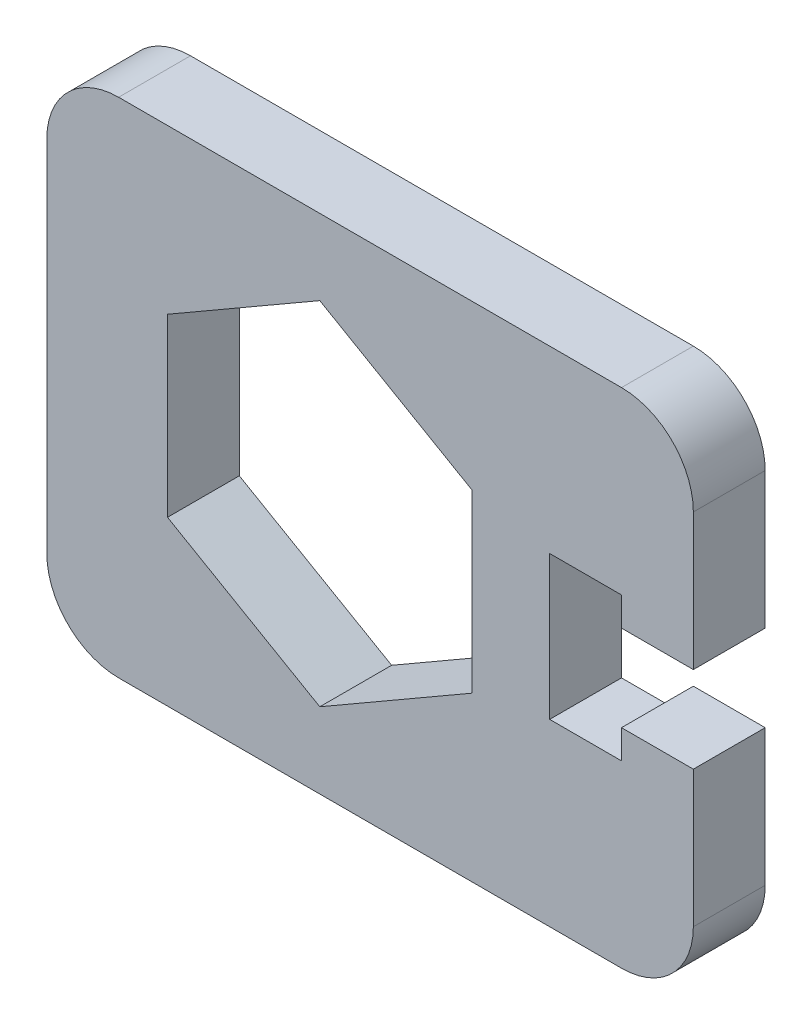
SolidWorks part; units mm, degrees
material "Acier non allié"
ref_plane "Plan de face" through (0, 0, 0) normal (0, 0, 1) x (1, 0, 0)
ref_plane "Plan de dessus" through (0, 0, 0) normal (0, 1, 0) x (1, 0, 0)
ref_plane "Plan de droite" through (0, 0, 0) normal (1, 0, 0) x (0, 0, -1)
sketch "Esquisse1" plane through (0, 0, 0) normal (0, 0, 1) x (1, 0, 0)
  line L0 (22.5, 3) -> (22.5, 17.5)
  line L1 (22.5, -17.5) -> (-22.5, -17.5)
  line L2 (22.5, -17.5) -> (22.5, -3)
  line L3 (22.5, 17.5) -> (-22.5, 17.5)
  line L4 (-22.5, -17.5) -> (-22.5, 17.5)
  line L5 (22.5, -17.5) -> (-22.5, 17.5) construction
  line L6 (22.5, 17.5) -> (-22.5, -17.5) construction
  line L7 (17.5, -3) -> (22.5, -3)
  line L9 (17.5, 3) -> (22.5, 3)
  line L11 (17.5, -3) -> (22.5, 3) construction
  line L12 (17.5, 3) -> (22.5, -3) construction
  line L13 (17.5, 3) -> (17.5, 5)
  line L14 (7.1, 6.1199) -> (-3.5, 12.2398)
  line L15 (-3.5, 12.2398) -> (-14.1, 6.1199)
  line L16 (-14.1, 6.1199) -> (-14.1, -6.1199)
  line L17 (-14.1, -6.1199) -> (-3.5, -12.2398)
  line L18 (-3.5, -12.2398) -> (7.1, -6.1199)
  line L19 (7.1, -6.1199) -> (7.1, 6.1199)
  line L20 (17.5, 5) -> (12.5, 5)
  line L21 (12.5, 5) -> (12.5, -5)
  line L22 (12.5, -5) -> (17.5, -5)
  line L23 (17.5, -5) -> (17.5, -3)
  circle A0 centre (-3.5, 0) radius 10.6 construction
  point P0 (0, 0)
  point P6 (20, 0)
extrude "Boss.-Extru.1" add sketch "Esquisse1" along normal mid plane 5
fillet "Congé1" radius 5 4 edges at (22.5, 17.5, 0) (22.5, -17.5, 0) (-22.5, -17.5, 0) (-22.5, 17.5, 0)
equation "\"D8@Esquisse1\"=\"D4@Esquisse1\"/2"
